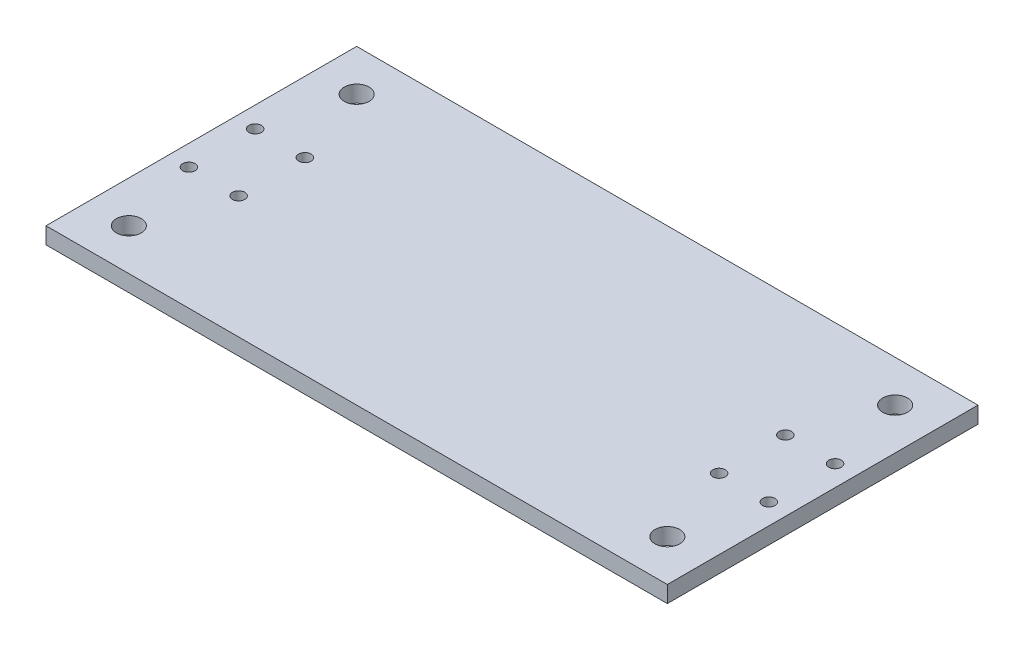
SolidWorks part; units mm, degrees
ref_plane "Front Plane" through (0, 0, 0) normal (0, 0, 1) x (1, 0, 0)
ref_plane "Top Plane" through (0, 0, 0) normal (0, 1, 0) x (1, 0, 0)
ref_plane "Right Plane" through (0, 0, 0) normal (1, 0, 0) x (0, 0, -1)
sketch "Sketch1" plane through (0, 0, 0) normal (0, 1, 0) x (1, 0, 0)
  line L0 (0, 37.5) -> (0, -37.5) construction
  line L1 (-75, -37.5) -> (75, -37.5)
  line L2 (-75, -37.5) -> (-75, 37.5)
  line L3 (-75, 37.5) -> (75, 37.5)
  line L4 (75, -37.5) -> (75, 37.5)
  line L5 (-75, -37.5) -> (75, 37.5) construction
  line L6 (-75, 37.5) -> (75, -37.5) construction
  line L7 (-75, 0) -> (75, 0) construction
  line L8 (-70, 37.5) -> (-70, -37.5) construction
  line L9 (70, 37.5) -> (70, -37.5) construction
  line L10 (-70, 8) -> (0, 8) construction
  line L11 (-70, -8) -> (0, -8) construction
  line L12 (-64, 8) -> (-64, -8) construction
  line L13 (-65, 37.5) -> (-65, -37.5) construction
  line L14 (-70, 27.5) -> (70, 27.5) construction
  line L15 (70, -27.5) -> (-65, -27.5) construction
  circle A4 centre (-70, 8) radius 1.5
  circle A5 centre (-70, -8) radius 1.5
  circle A6 centre (-58, -8) radius 1.5
  circle A7 centre (-58, 8) radius 1.5
  circle A8 centre (58, -8) radius 1.5
  circle A9 centre (70, -8) radius 1.5
  circle A10 centre (58, 8) radius 1.5
  circle A11 centre (70, 8) radius 1.5
  circle A12 centre (-65, 27.5) radius 3
  circle A13 centre (65, 27.5) radius 3
  circle A14 centre (-65, -27.5) radius 3
  circle A15 centre (65, -27.5) radius 3
  point P0 (0, 0)
  dimension "D3" = 10
  dimension "D6" = 3
  dimension "D10" = 6
  dimension "D1" = 150
  dimension "D2" = 75
  dimension "D4" = 10
  dimension "D5" = 5
  dimension "D7" = 8
  dimension "D8" = 6
  dimension "D9" = 10
  dimension "D11" = 6
  dimension "D12" = 29.5
  dimension "D13" = 16
extrude "Boss-Extrude1" add sketch "Sketch1" along normal blind 4
